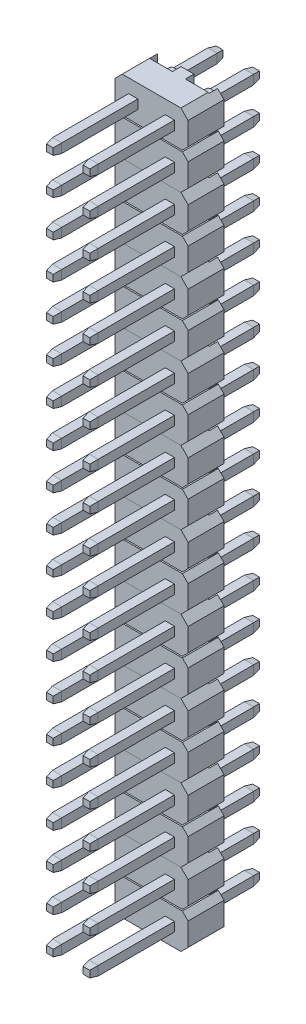
SolidWorks part; units mm, degrees
ref_plane "Płaszczyzna przednia" through (0, 0, 0) normal (0, 0, 1) x (1, 0, 0)
ref_plane "Płaszczyzna górna" through (0, 0, 0) normal (0, 1, 0) x (1, 0, 0)
ref_plane "Płaszczyzna prawa" through (0, 0, 0) normal (1, 0, 0) x (0, 0, -1)
sketch "Sketch1" plane through (0, 0, 0) normal (0, 0, 1) x (1, 0, 0)
  line L1 (1.27, 1.27) -> (-1.27, 1.27) construction
  line L2 (1.27, 1.27) -> (1.27, -1.27) construction
  line L3 (1.27, -1.27) -> (-1.27, -1.27) construction
  line L4 (-1.27, 1.27) -> (-1.27, -1.27) construction
  line L5 (1.27, 1.27) -> (-1.27, -1.27) construction
  line L6 (1.27, -1.27) -> (-1.27, 1.27) construction
  line L7 (-0.95, 0.95) -> (-1.59, 0.95)
  line L8 (-0.95, 0.95) -> (-0.95, 1.59)
  line L9 (-0.95, 1.59) -> (-1.59, 1.59)
  line L10 (-1.59, 0.95) -> (-1.59, 1.59)
  line L11 (-0.95, 0.95) -> (-1.59, 1.59) construction
  line L12 (-0.95, 1.59) -> (-1.59, 0.95) construction
  line L13 (-0.95, -0.95) -> (-1.59, -0.95)
  line L14 (-0.95, -0.95) -> (-0.95, -1.59)
  line L15 (-0.95, -1.59) -> (-1.59, -1.59)
  line L16 (-1.59, -0.95) -> (-1.59, -1.59)
  line L17 (-0.95, -0.95) -> (-1.59, -1.59) construction
  line L18 (-0.95, -1.59) -> (-1.59, -0.95) construction
  line L19 (0.95, 0.95) -> (1.59, 0.95)
  line L20 (0.95, 0.95) -> (0.95, 1.59)
  line L21 (0.95, 1.59) -> (1.59, 1.59)
  line L22 (1.59, 0.95) -> (1.59, 1.59)
  line L23 (0.95, 0.95) -> (1.59, 1.59) construction
  line L24 (0.95, 1.59) -> (1.59, 0.95) construction
  line L25 (0.95, -1.59) -> (1.59, -1.59)
  line L26 (0.95, -1.59) -> (0.95, -0.95)
  line L27 (0.95, -0.95) -> (1.59, -0.95)
  line L28 (1.59, -1.59) -> (1.59, -0.95)
  line L29 (0.95, -1.59) -> (1.59, -0.95) construction
  line L30 (0.95, -0.95) -> (1.59, -1.59) construction
  point P0 (0, 0)
extrude "Boss-Extrude1" add sketch "Sketch1" along normal blind 5.3
sketch "Sketch2" plane through (0, 0, 5.3) normal (0, 0, 1) x (1, 0, 0)
  line L4 (-1.59, -0.95) -> (-1.59, -1.59)
  line L5 (-1.59, -1.59) -> (-0.95, -1.59)
  line L6 (-0.95, -1.59) -> (-0.95, -0.95)
  line L7 (-0.95, -0.95) -> (-1.59, -0.95)
  line L8 (-1.59, -0.95) -> (-1.59, -1.59)
  line L9 (-1.59, -1.59) -> (-0.95, -1.59)
  line L10 (-0.95, -1.59) -> (-0.95, -0.95)
  line L11 (-0.95, -0.95) -> (-1.59, -0.95)
  line L12 (-1.59, 1.59) -> (-1.59, 0.95)
  line L13 (-1.59, 0.95) -> (-0.95, 0.95)
  line L14 (-0.95, 0.95) -> (-0.95, 1.59)
  line L15 (-0.95, 1.59) -> (-1.59, 1.59)
  line L16 (-1.59, 1.59) -> (-1.59, 0.95)
  line L17 (-1.59, 0.95) -> (-0.95, 0.95)
  line L18 (-0.95, 0.95) -> (-0.95, 1.59)
  line L19 (-0.95, 1.59) -> (-1.59, 1.59)
  line L20 (1.59, -1.59) -> (1.59, -0.95)
  line L21 (1.59, -0.95) -> (0.95, -0.95)
  line L22 (0.95, -0.95) -> (0.95, -1.59)
  line L23 (0.95, -1.59) -> (1.59, -1.59)
  line L24 (1.59, -1.59) -> (1.59, -0.95)
  line L25 (1.59, -0.95) -> (0.95, -0.95)
  line L26 (0.95, -0.95) -> (0.95, -1.59)
  line L27 (0.95, -1.59) -> (1.59, -1.59)
  line L28 (1.59, 0.95) -> (1.59, 1.59)
  line L29 (1.59, 1.59) -> (0.95, 1.59)
  line L30 (0.95, 1.59) -> (0.95, 0.95)
  line L31 (0.95, 0.95) -> (1.59, 0.95)
  line L32 (1.59, 0.95) -> (1.59, 1.59)
  line L33 (1.59, 1.59) -> (0.95, 1.59)
  line L34 (0.95, 1.59) -> (0.95, 0.95)
  line L35 (0.95, 0.95) -> (1.59, 0.95)
  dimension "D1" = 0
  dimension "D2" = 0
  dimension "D3" = 0
  dimension "D4" = 0
extrude "Boss-Extrude2" add sketch "Sketch2" along normal blind 0.5 draft 10
sketch "Sketch3" plane through (0, 0, 0) normal (0, 0, 1) x (1, 0, 0)
  line L1 (-2.04, 2.54) -> (2.04, 2.54)
  line L2 (-2.54, 2.04) -> (-2.54, -2.04)
  line L3 (-2.04, -2.54) -> (2.04, -2.54)
  line L4 (2.54, 2.04) -> (2.54, -2.04)
  line L5 (-2.54, 2.54) -> (2.54, -2.54) construction
  line L6 (-2.54, -2.54) -> (2.54, 2.54) construction
  line L24 (-2.54, -2.04) -> (-2.04, -2.54)
  line L25 (2.04, -2.54) -> (2.54, -2.04)
  line L26 (2.04, 2.54) -> (2.54, 2.04)
  line L27 (-2.54, 2.04) -> (-2.04, 2.54)
  point P0 (0, 0)
extrude "Boss-Extrude3" add sketch "Sketch3" against normal blind 2.5 separate body
sketch "Sketch5" plane through (0, 0, -2.5) normal (0, 0, -1) x (-1, 0, 0)
  line L0 (-0.45, -2.54) -> (-0.45, 2.54)
  line L1 (2.04, -2.54) -> (-2.04, -2.54) construction
  line L2 (-2.04, 2.54) -> (2.04, 2.54) construction
  line L3 (-2.09, -2.54) -> (-2.09, 2.54)
  line L4 (-2.54, -2.04) -> (-2.54, 2.04) construction
  line L5 (-0.95, -0.95) -> (-0.95, -1.59) construction
  line L7 (0, -2.54) -> (0, -3.101) construction
  line L8 (2.09, -2.54) -> (2.09, 2.54)
  line L9 (0.45, -2.54) -> (0.45, 2.54)
  line L10 (2.09, -2.54) -> (0.45, -2.54)
  line L11 (-0.45, -2.54) -> (-2.09, -2.54)
  line L12 (2.09, 2.54) -> (0.45, 2.54)
  line L13 (-0.45, 2.54) -> (-2.09, 2.54)
  dimension "D1" = 0.45
  dimension "D2" = 0.5
extrude "Cut-Extrude1" cut sketch "Sketch5" against normal blind 0.6
sketch "Sketch6" plane through (0, 0, 0) normal (0, 0, 1) x (1, 0, 0)
  line L0 (2.54, 0) -> (-2.54, 0) construction
  line L1 (2.54, -2.04) -> (2.54, 2.04) construction
  line L2 (-2.54, 2.04) -> (-2.54, -2.04) construction
  line L3 (-2.54, 0.05) -> (-2.54, -0.05)
  line L4 (-2.54, 0.05) -> (2.54, 0.05)
  line L5 (2.54, 0.05) -> (2.54, -0.05)
  line L6 (2.54, -0.05) -> (-2.54, -0.05)
  dimension "D1" = 0.1
extrude "Cut-Extrude2" cut sketch "Sketch6" against normal through all
sketch "Sketch7" plane through (0, 0, 0) normal (0, 0, 1) x (1, 0, 0)
  line L0 (2.54, 0.45) -> (2.14, 0.05)
  line L1 (2.54, 0.05) -> (2.54, 2.04) construction
  line L2 (2.54, 0.05) -> (-2.54, 0.05) construction
  line L3 (2.14, 0.05) -> (2.54, 0.05)
  line L4 (2.54, 0.05) -> (2.54, 0.45)
  line L5 (2.54, -0.05) -> (2.14, -0.05)
  line L6 (-2.54, -0.05) -> (2.54, -0.05) construction
  line L7 (2.14, -0.05) -> (2.54, -0.45)
  line L8 (2.54, -2.04) -> (2.54, -0.05) construction
  line L9 (2.54, -0.45) -> (2.54, -0.05)
  line L10 (0, -0.05) -> (0, 3.4542) construction
  line L11 (-2.54, -0.45) -> (-2.54, -0.05)
  line L12 (-2.14, -0.05) -> (-2.54, -0.45)
  line L13 (-2.54, -0.05) -> (-2.14, -0.05)
  line L14 (-2.54, 0.05) -> (-2.54, 0.45)
  line L15 (-2.14, 0.05) -> (-2.54, 0.05)
  line L16 (-2.54, 0.45) -> (-2.14, 0.05)
  dimension "D1" = 0.4
  dimension "D2" = 0.4
  dimension "D3" = 0.4
extrude "Cut-Extrude3" cut sketch "Sketch7" against normal through all
sketch "Sketch8" plane through (0, 0, -1.9) normal (0, 0, -1) x (-1, 0, 0)
  line L0 (1.59, -1.59) -> (0.95, -1.59)
  line L1 (0.95, -1.59) -> (0.95, -0.95)
  line L2 (0.95, -0.95) -> (1.59, -0.95)
  line L3 (1.59, -0.95) -> (1.59, -1.59)
  line L12 (0.95, 1.59) -> (1.59, 1.59) construction
  line L13 (0.95, 0.95) -> (0.95, 1.59) construction
  line L14 (1.59, 1.59) -> (1.59, 0.95) construction
  line L15 (1.59, 0.95) -> (0.95, 0.95) construction
  line L16 (-0.95, 0.95) -> (-1.59, 0.95) construction
  line L17 (-0.95, 1.59) -> (-0.95, 0.95) construction
  line L18 (-1.59, 1.59) -> (-0.95, 1.59) construction
  line L19 (-1.59, 0.95) -> (-1.59, 1.59) construction
  line L20 (-1.59, -0.95) -> (-0.95, -0.95) construction
  line L21 (-1.59, -1.59) -> (-1.59, -0.95) construction
  line L22 (-0.95, -0.95) -> (-0.95, -1.59) construction
  line L23 (-0.95, -1.59) -> (-1.59, -1.59) construction
  line L32 (0.95, 1.59) -> (1.59, 1.59)
  line L33 (0.95, 0.95) -> (0.95, 1.59)
  line L34 (1.59, 1.59) -> (1.59, 0.95)
  line L35 (1.59, 0.95) -> (0.95, 0.95)
  line L36 (-0.95, 0.95) -> (-1.59, 0.95)
  line L37 (-0.95, 1.59) -> (-0.95, 0.95)
  line L38 (-1.59, 1.59) -> (-0.95, 1.59)
  line L39 (-1.59, 0.95) -> (-1.59, 1.59)
  line L40 (-1.59, -0.95) -> (-0.95, -0.95)
  line L41 (-1.59, -1.59) -> (-1.59, -0.95)
  line L42 (-0.95, -0.95) -> (-0.95, -1.59)
  line L43 (-0.95, -1.59) -> (-1.59, -1.59)
extrude "Boss-Extrude4" add sketch "Sketch8" along normal blind 3.6 separate body
sketch "Sketch9" plane through (0, 0, -5.5) normal (0, 0, -1) x (-1, 0, 0)
  line L4 (0.95, 1.59) -> (0.95, 0.95)
  line L5 (0.95, 0.95) -> (1.59, 0.95)
  line L6 (1.59, 0.95) -> (1.59, 1.59)
  line L7 (1.59, 1.59) -> (0.95, 1.59)
  line L8 (0.95, 1.59) -> (0.95, 0.95)
  line L9 (0.95, 0.95) -> (1.59, 0.95)
  line L10 (1.59, 0.95) -> (1.59, 1.59)
  line L11 (1.59, 1.59) -> (0.95, 1.59)
  line L12 (1.59, -1.59) -> (1.59, -0.95)
  line L13 (1.59, -0.95) -> (0.95, -0.95)
  line L14 (0.95, -0.95) -> (0.95, -1.59)
  line L15 (0.95, -1.59) -> (1.59, -1.59)
  line L16 (1.59, -1.59) -> (1.59, -0.95)
  line L17 (1.59, -0.95) -> (0.95, -0.95)
  line L18 (0.95, -0.95) -> (0.95, -1.59)
  line L19 (0.95, -1.59) -> (1.59, -1.59)
  line L20 (-1.59, -0.95) -> (-1.59, -1.59)
  line L21 (-1.59, -1.59) -> (-0.95, -1.59)
  line L22 (-0.95, -1.59) -> (-0.95, -0.95)
  line L23 (-0.95, -0.95) -> (-1.59, -0.95)
  line L24 (-1.59, -0.95) -> (-1.59, -1.59)
  line L25 (-1.59, -1.59) -> (-0.95, -1.59)
  line L26 (-0.95, -1.59) -> (-0.95, -0.95)
  line L27 (-0.95, -0.95) -> (-1.59, -0.95)
  line L28 (-0.95, 0.95) -> (-0.95, 1.59)
  line L29 (-0.95, 1.59) -> (-1.59, 1.59)
  line L30 (-1.59, 1.59) -> (-1.59, 0.95)
  line L31 (-1.59, 0.95) -> (-0.95, 0.95)
  line L32 (-0.95, 0.95) -> (-0.95, 1.59)
  line L33 (-0.95, 1.59) -> (-1.59, 1.59)
  line L34 (-1.59, 1.59) -> (-1.59, 0.95)
  line L35 (-1.59, 0.95) -> (-0.95, 0.95)
  dimension "D1" = 0
  dimension "D2" = 0
  dimension "D3" = 0
  dimension "D4" = 0
extrude "Boss-Extrude5" add sketch "Sketch9" along normal blind 0.5 draft 10
pattern_linear "LPattern1" count 10 spacing 5.08 along (0, -1, 0) of bodies 106 119 108 121 113 105 107 120 122 114
sketch "Sketch10" plane through (0, 0, -1.9) normal (0, 0, -1) x (-1, 0, 0)
  line L0 (-1.27, 1.0382) -> (-1.27, 1.5018) construction
  line L1 (-1.5018, 1.0382) -> (-1.0382, 1.0382) construction
  line L2 (-1.0382, 1.5018) -> (-1.5018, 1.5018) construction
  line L3 (1.27, 1.5018) -> (1.27, 1.0382) construction
  line L4 (1.5018, 1.5018) -> (1.0382, 1.5018) construction
  line L5 (1.0382, 1.0382) -> (1.5018, 1.0382) construction
  circle A0 centre (-1.27, 1.27) radius 0.56
  circle A1 centre (1.27, 1.27) radius 0.56
extrude "Boss-Extrude6" add sketch "Sketch10" along normal blind 1 separate body
